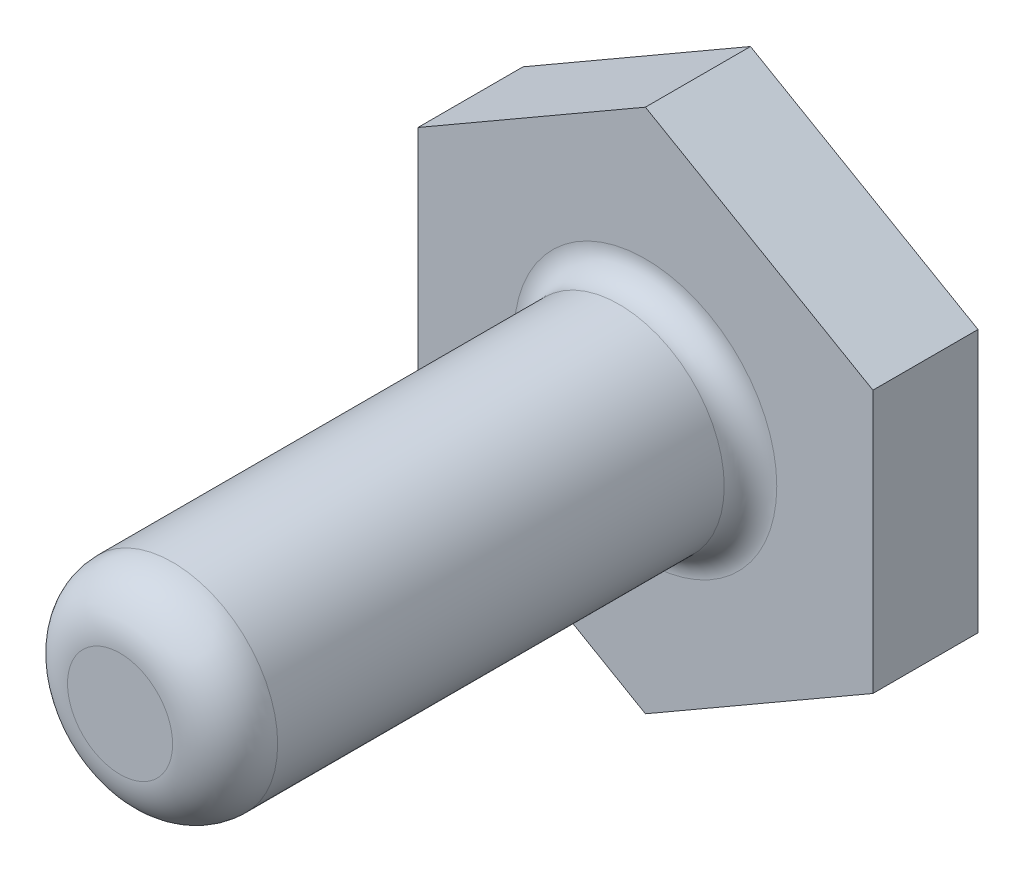
SolidWorks part; units mm, degrees
ref_plane "Front Plane" through (0, 0, 0) normal (0, 0, 1) x (1, 0, 0)
ref_plane "Top Plane" through (0, 0, 0) normal (0, 1, 0) x (1, 0, 0)
ref_plane "Right Plane" through (0, 0, 0) normal (1, 0, 0) x (0, 0, -1)
sketch "Sketch1" plane through (0, 0, 0) normal (0, 0, 1) x (1, 0, 0)
  line L1 (-0.3531, 3.1897) -> (-0.3531, 13.1897)
  line L2 (-0.3531, 13.1897) -> (-9.0134, 18.1897)
  line L3 (-9.0134, 18.1897) -> (-17.6736, 13.1897)
  line L4 (-17.6736, 13.1897) -> (-17.6736, 3.1897)
  line L5 (-17.6736, 3.1897) -> (-9.0134, -1.8103)
  line L6 (-9.0134, -1.8103) -> (-0.3531, 3.1897)
  circle A0 centre (-9.0134, 8.1897) radius 8.6603 construction
  dimension "D1" = 10
  dimension "D2" = 10
extrude "Boss-Extrude2" add sketch "Sketch1" along normal blind 4 contours L3 L4 L5 L6 L1 L2
sketch "Sketch4" plane through (0, 0, 4) normal (0, 0, 1) x (1, 0, 0)
  circle A1 centre (-9.0134, 8.1897) radius 4
extrude "Boss-Extrude3" add sketch "Sketch4" along normal blind 20
fillet "Fillet1" radius 2 1 edges at (-5.0134, 8.1897, 24)
fillet "Fillet3" radius 1 1 edges at (-5.0134, 8.1897, 4)
